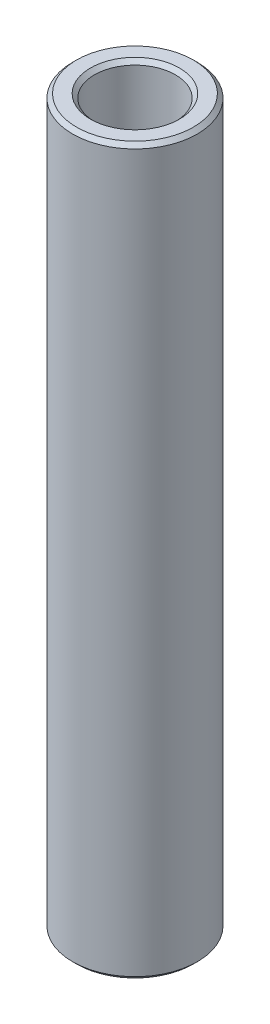
SolidWorks part; units mm, degrees
ref_plane "Front Plane" through (0, 0, 0) normal (0, 0, 1) x (1, 0, 0)
ref_plane "Top Plane" through (0, 0, 0) normal (0, 1, 0) x (1, 0, 0)
ref_plane "Right Plane" through (0, 0, 0) normal (1, 0, 0) x (0, 0, -1)
sketch "Sketch1" plane through (0, 0, 0) normal (0, 0, 1) x (1, 0, 0)
  line L0 (0, 9.6156) -> (0, -9.6156) construction
  line L1 (1.3, -11.637) -> (2, -11.637)
  line L2 (2, -11.637) -> (2, 11.637)
  line L3 (2, 11.637) -> (1.3, 11.637)
  line L4 (1.3, 11.637) -> (1.3, -11.637)
  point P7 (1.3, 0)
  dimension "D1" = 23.274
  dimension "D2" = 4
  dimension "D3" = 2.6
revolve "Revolve1" add sketch "Sketch1" angle 360 about L0
chamfer "Chamfer1" distance 0.127 angle 45 4 edges at (0, -11.637, 1.3) (0, -11.637, 2) (0, 11.637, 2) (0, 11.637, 1.3)
